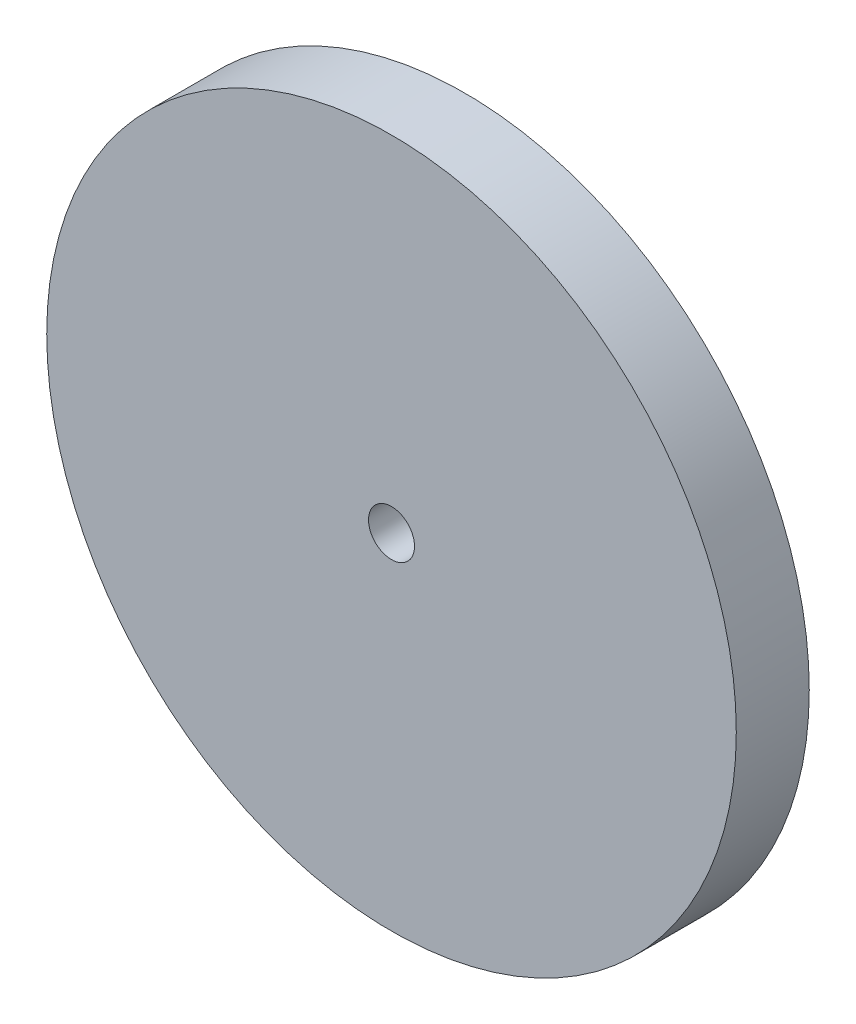
SolidWorks part; units mm, degrees
ref_plane "Front Plane" through (0, 0, 0) normal (0, 0, 1) x (1, 0, 0)
ref_plane "Top Plane" through (0, 0, 0) normal (0, 1, 0) x (1, 0, 0)
ref_plane "Right Plane" through (0, 0, 0) normal (1, 0, 0) x (0, 0, -1)
sketch "Sketch1" plane through (0, 0, 0) normal (0, 0, 1) x (1, 0, 0)
  circle A0 centre (0, 0) radius 15
  dimension "D1" = 30
extrude "Boss-Extrude1" add sketch "Sketch1" along normal blind 3.175
sketch "Sketch2" plane through (0, 0, 3.175) normal (0, 0, 1) x (1, 0, 0)
  line L0 (15, 0) -> (0, 0)
  circle A0 centre (0, 0) radius 15 construction
  circle A1 centre (0, 0) radius 1
  circle A2 centre (0, 0) radius 4.9004
  circle A3 centre (0, 0) radius 8.5658
  circle A4 centre (0, 0) radius 11.9344
  dimension "D1" = 2
  dimension "D2" = 9.8007
  dimension "D3" = 17.1316
  dimension "D4" = 23.8687
extrude "Cut-Extrude1" cut sketch "Sketch2" against normal blind 3.175 contours A1
